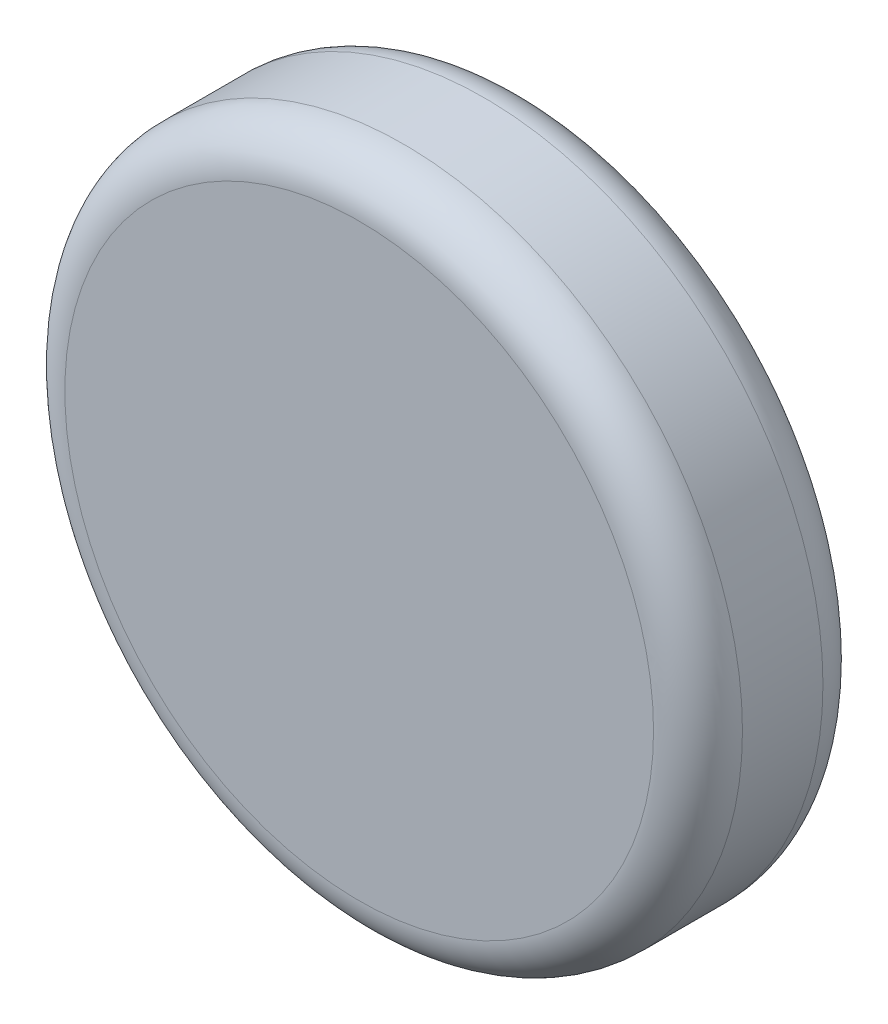
SolidWorks part; units mm, degrees
ref_plane "Front Plane" through (0, 0, 0) normal (0, 0, 1) x (1, 0, 0)
ref_plane "Top Plane" through (0, 0, 0) normal (0, 1, 0) x (1, 0, 0)
ref_plane "Right Plane" through (0, 0, 0) normal (1, 0, 0) x (0, 0, -1)
sketch "Sketch1" plane through (0, 0, 0) normal (0, 0, 1) x (1, 0, 0)
  circle A0 centre (0, 0) radius 152.4
  dimension "D1" = 304.8
extrude "Boss-Extrude1" add sketch "Sketch1" along normal blind 76.2
fillet "Fillet1" radius 20 2 edges at (152.4, 0, 0) (152.4, 0, 76.2)
sketch "Sketch2" plane through (0, 0, 0) normal (0, 0, -1) x (-1, 0, 0)
  circle A0 centre (0, 0) radius 15
  circle A1 centre (0, 0) radius 7.5
  dimension "D1" = 30
  dimension "D2" = 7.5
extrude "Boss-Extrude2" add sketch "Sketch2" along normal blind 45
sketch "Sketch4" plane through (0, 0, 0) normal (1, 0, 0) x (0, 0, -1)
  line L0 (45, -15) -> (45, 15) construction
  circle A0 centre (30, 0) radius 3.1
  dimension "D1" = 6.2
  dimension "D2" = 15
extrude "Cut-Extrude1" cut sketch "Sketch4" against normal through all both and the other way through all
